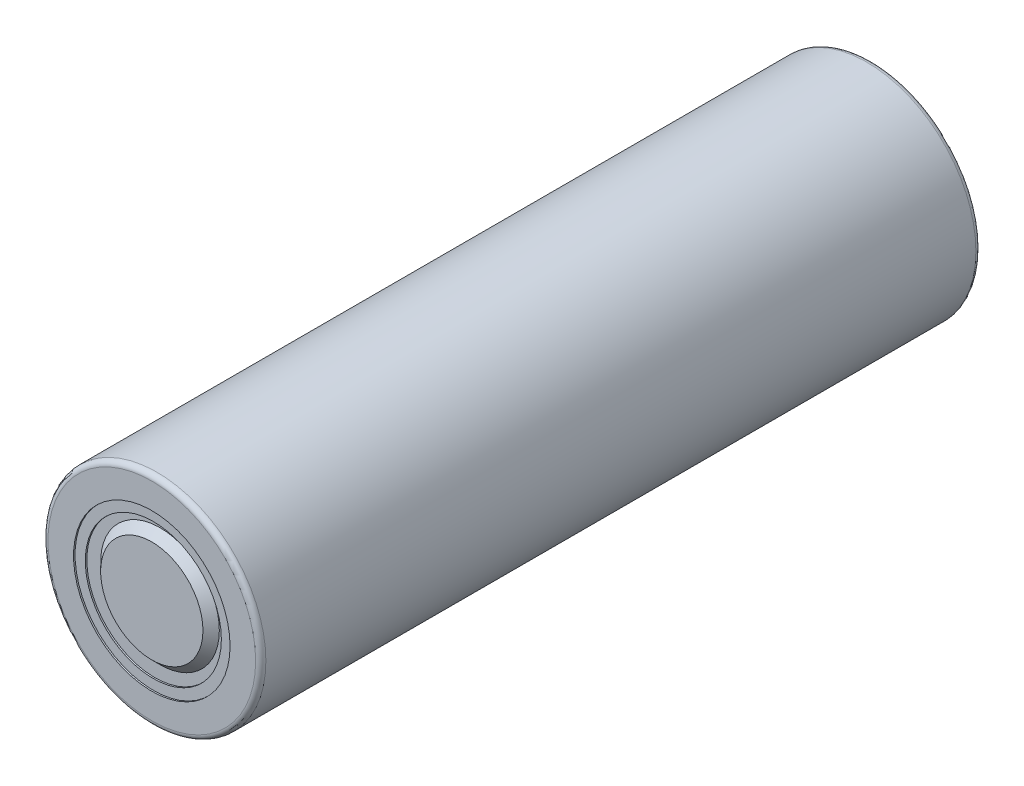
SolidWorks part; units mm, degrees
ref_plane "Front Plane" through (0, 0, 0) normal (0, 0, 1) x (1, 0, 0)
ref_plane "Top Plane" through (0, 0, 0) normal (0, 1, 0) x (1, 0, 0)
ref_plane "Right Plane" through (0, 0, 0) normal (1, 0, 0) x (0, 0, -1)
sketch "Sketch1" plane through (0, 0, 0) normal (0, 0, 1) x (1, 0, 0)
  circle A0 centre (0, 0) radius 10.65
  dimension "D1" = 21.3
extrude "Boss-Extrude1" add sketch "Sketch1" along normal blind 70.4
sketch "Sketch2" plane through (0, 0, 0) normal (0, 0, 1) x (1, 0, 0)
  circle A0 centre (0, 0) radius 8.65
  circle A2 centre (0, 0) radius 10.65 construction
  dimension "D1" = 2
extrude "Cut-Extrude1" cut sketch "Sketch2" along normal blind 0.2
sketch "Sketch3" plane through (0, 0, 0) normal (0, 1, 0) x (1, 0, 0)
  line L1 (-10.65, -70.4) -> (10.65, -70.4) construction
  line L16 (0, -70.4) -> (0, 0) construction
  line L17 (-9.15, -70.1) -> (-9.15, -69.6)
  line L18 (-5.8, -69.6) -> (-5, -70.4)
  line L19 (-5, -70.4) -> (-7.65, -70.4)
  line L20 (-7.65, -70.4) -> (-7.65, -70.25)
  line L21 (-7.65, -70.25) -> (-6.65, -70.25)
  line L22 (-6.65, -70.25) -> (-6.65, -70.1)
  line L23 (-6.65, -70.1) -> (-9.15, -70.1)
  line L24 (-9.15, -69.6) -> (-5.8, -69.6)
  point P0 (0, -70.4)
  dimension "D1" = 2.65
  dimension "D2" = 1
  dimension "D3" = 1.5
  dimension "D4" = 5
  dimension "D5" = 0.15
  dimension "D6" = 0.15
  dimension "D7" = 0.5
  dimension "D8" = 45
revolve "Cut-Revolve1" cut sketch "Sketch3" angle 360 about L16
fillet "Fillet1" radius 0.5 2 edges at (10.65, 0, 0) (10.65, 0, 70.4)
